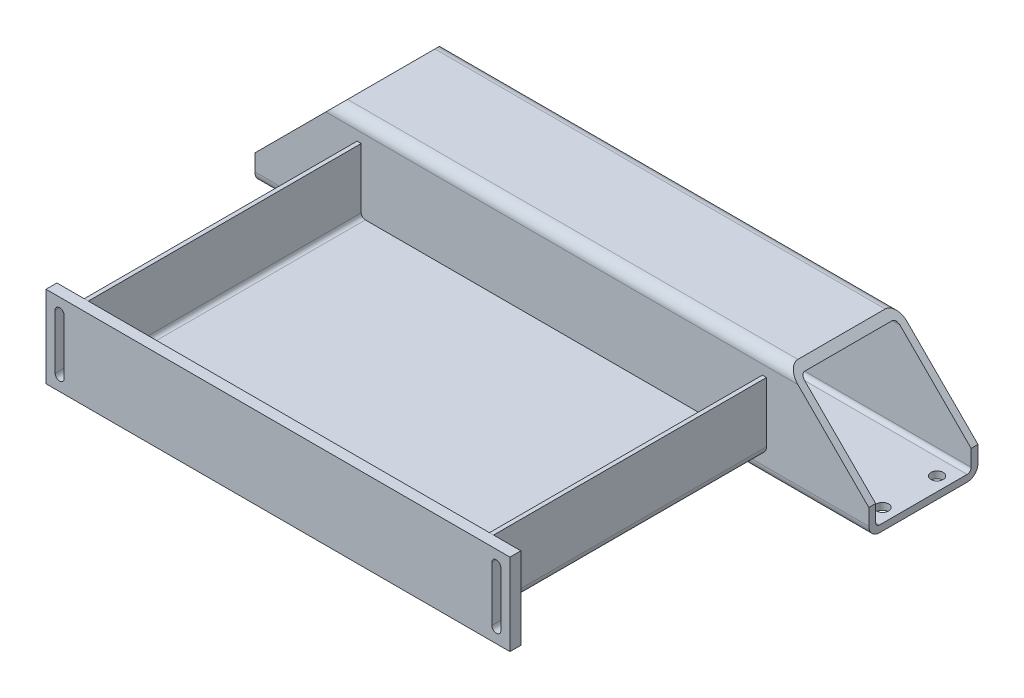
SolidWorks part; units mm, degrees
other "Muster (Pos 3 Laser 3mm S235 1x)"
other "Muster (Pos 2 Laser 8mm S235 1x"
other "Muster (Pos 4 Laser 3mm S235 1x)"
other "Muster (Pos 1 Rohrlaser S235 1x)"
ref_plane "Ebene vorne" through (0, 0, 0) normal (0, 0, 1) x (1, 0, 0)
ref_plane "Ebene oben" through (0, 0, 0) normal (0, 1, 0) x (1, 0, 0)
ref_plane "Ebene rechts" through (0, 0, 0) normal (1, 0, 0) x (0, 0, -1)
sketch "Skizze1" plane through (0, 0, 0) normal (0, 0, 1) x (1, 0, 0)
  line L0 (0, 0) -> (0, 100.5526) construction
  line L1 (-150, 50) -> (-150, 6)
  line L2 (-144, 0) -> (144, 0)
  line L4 (144, 3) -> (-144, 3)
  line L5 (-147, 6) -> (-147, 50)
  line L6 (-147, 50) -> (-150, 50)
  line L7 (150, 50) -> (150, 6)
  line L8 (147, 50) -> (150, 50)
  line L9 (147, 6) -> (147, 50)
  arc A0 (-144, 3) -> (-147, 6) centre (-144, 6) cw
  arc A1 (-150, 6) -> (-144, 0) centre (-144, 6) ccw
  arc A2 (144, 3) -> (147, 6) centre (144, 6) ccw
  arc A3 (150, 6) -> (144, 0) centre (144, 6) cw
  dimension "D1" = 3
  dimension "D2" = 6
  dimension "D3" = 50
  dimension "D4" = 150
extrude "Aufsatz-Linear austragen1" add sketch "Skizze1" along normal mid plane 200
sketch "Skizze2" plane through (0, 0, 100) normal (0, 0, 1) x (1, 0, 0)
  line L0 (-147, 50) -> (-150, 50) construction
  line L1 (-170, 50) -> (170, 50)
  line L2 (-170, 50) -> (-170, -10)
  line L3 (-170, -10) -> (170, -10)
  line L4 (170, 50) -> (170, -10)
  line L5 (-150, 50) -> (-150, 6) construction
  line L6 (150, 6) -> (150, 50) construction
  line L7 (-144, 0) -> (144, 0) construction
  dimension "D1" = 20
  dimension "D2" = 20
  dimension "D3" = 10
extrude "Aufsatz-Linear austragen2" add sketch "Skizze2" along normal blind 8 separate body
sketch "Skizze4" plane through (0, 0, 0) normal (1, 0, 0) x (0, 0, -1)
  line L0 (-100, 45) -> (-95, 45)
  line L1 (-95, 45) -> (-58, 8)
  line L2 (-58, 8) -> (-58, 3)
  line L3 (-58, 3) -> (-100, 3)
  line L4 (-100, 3) -> (-100, 45)
  line L5 (-100, -10) -> (-100, 50) construction
  line L6 (-100, 3) -> (100, 3) construction
  line L7 (-108, 50) -> (-100, 50) construction
  dimension "D1" = 5
  dimension "D2" = 5
extrude "Aufsatz-Linear austragen3" add sketch "Skizze4" along normal mid plane 3 separate body
sketch "Skizze5" plane through (0, 0, 108) normal (0, 0, 1) x (1, 0, 0)
  line L0 (160, 0) -> (160, 40) construction
  line L1 (0, 0) -> (0, -43.4486) construction
  line L2 (163.3, 0) -> (163.3, 40)
  line L3 (156.7, 0) -> (156.7, 40)
  line L4 (170, -10) -> (170, 50) construction
  line L5 (170, 50) -> (-170, 50) construction
  line L6 (-170, -10) -> (170, -10) construction
  arc A0 (163.3, 0) -> (156.7, 0) centre (160, 0) cw
  arc A1 (163.3, 40) -> (156.7, 40) centre (160, 40) ccw
  dimension "D5" = 10
  dimension "D1" = 3.3
  dimension "D3" = 10
  dimension "D4" = 10
  dimension "D2" = 3.3
extrude "Schnitt-Linear austragen1" cut sketch "Skizze5" against normal through all
mirror "Spiegeln1" about plane through (0, 0, 0) normal (1, 0, 0) of "Schnitt-Linear austragen1"
sketch "Skizze6" plane through (0, 0, 0) normal (1, 0, 0) x (0, 0, -1)
  line L0 (100, 6) -> (100, 50) construction
  line L1 (108, -15) -> (172, -15)
  line L2 (100, -7) -> (100, 57)
  line L3 (108, 65) -> (172, 65)
  line L4 (180, -7) -> (180, 57)
  line L5 (-100, 0) -> (100, 0) construction
  line L6 (108, 60) -> (172, 60)
  line L7 (175, -7) -> (175, 57)
  line L8 (108, -10) -> (172, -10)
  line L9 (105, -7) -> (105, 57)
  arc A0 (108, -15) -> (100, -7) centre (108, -7) cw
  arc A1 (172, -15) -> (180, -7) centre (172, -7) ccw
  arc A2 (172, 65) -> (180, 57) centre (172, 57) cw
  arc A3 (100, 57) -> (108, 65) centre (108, 57) cw
  arc A4 (172, 60) -> (175, 57) centre (172, 57) cw
  arc A5 (172, -10) -> (175, -7) centre (172, -7) ccw
  arc A6 (108, -10) -> (105, -7) centre (108, -7) cw
  arc A7 (105, 57) -> (108, 60) centre (108, 57) cw
  point P6 (100, -15)
  point P13 (100, 65)
  dimension "D2" = 8
  dimension "D1" = 80
  dimension "D3" = 15
  dimension "D4" = 5
extrude "Aufsatz-Linear austragen4" add sketch "Skizze6" along normal mid plane 450
sketch "Skizze7" plane through (0, 0, -180) normal (0, 0, -1) x (-1, 0, 0)
  line L0 (-225, 5) -> (-165, 65)
  line L1 (-225, -7) -> (-225, 57) construction
  line L2 (-225, 65) -> (225, 65) construction
  line L3 (-165, 65) -> (-225, 65)
  line L4 (-225, 65) -> (-225, 5)
  line L5 (0, 0) -> (0, 95.6168) construction
  line L6 (225, 65) -> (225, 5)
  line L7 (165, 65) -> (225, 65)
  line L8 (225, 5) -> (165, 65)
  dimension "D1" = 60
extrude "Schnitt-Linear austragen2" cut sketch "Skizze7" against normal through all
sketch "Skizze8" plane through (0, -15, 0) normal (0, -1, 0) x (1, 0, 0)
  line L0 (225, -108) -> (225, -172) construction
  line L1 (0, 0) -> (0, -140) construction
  line L2 (0, -140) -> (225, -140) construction
  circle A0 centre (215, -160) radius 4.5
  circle A1 centre (215, -120) radius 4.5
  circle A2 centre (-215, -160) radius 4.5
  circle A3 centre (-215, -120) radius 4.5
  dimension "D1" = 9
  dimension "D3" = 40
  dimension "D2" = 10
extrude "Schnitt-Linear austragen3" cut sketch "Skizze8" against normal through all
